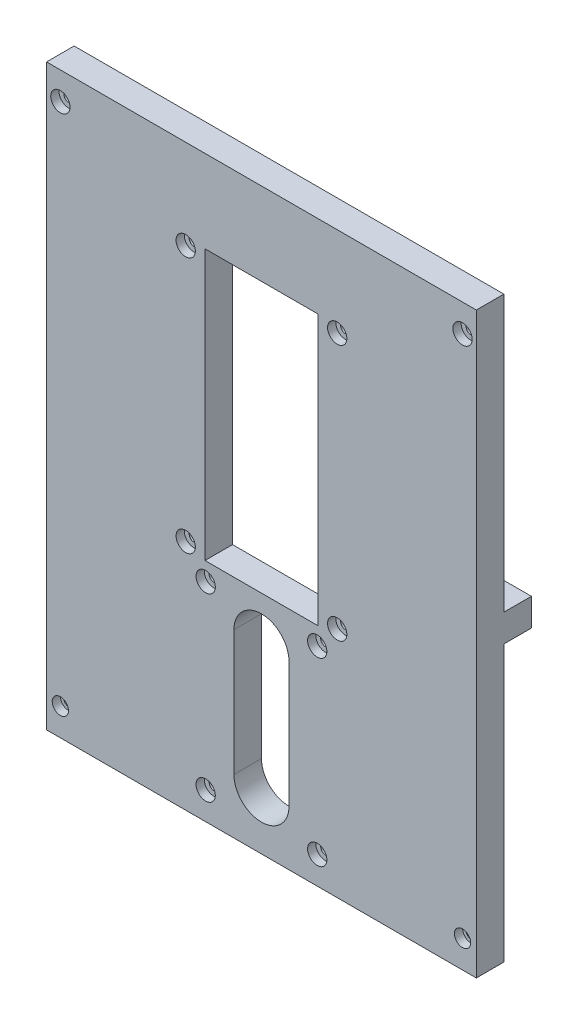
SolidWorks part; units mm, degrees
ref_plane "Płaszczyzna przednia" through (0, 0, 0) normal (0, 0, 1) x (1, 0, 0)
ref_plane "Płaszczyzna górna" through (0, 0, 0) normal (0, 1, 0) x (1, 0, 0)
ref_plane "Płaszczyzna prawa" through (0, 0, 0) normal (1, 0, 0) x (0, 0, -1)
sketch "Sketch1" plane through (0, 0, 0) normal (0, 0, 1) x (1, 0, 0)
  line L1 (-78, 105) -> (78, 105)
  line L2 (-78, 105) -> (-78, -105)
  line L3 (-78, -105) -> (78, -105)
  line L4 (78, 105) -> (78, -105)
  line L5 (-78, 105) -> (78, -105) construction
  line L6 (-78, -105) -> (78, 105) construction
  point P0 (0, 0)
  dimension "D1" = 156
  dimension "D2" = 210
extrude "Boss-Extrude1" add sketch "Sketch1" along normal blind 10
sketch "Sketch2" plane through (0, 0, 0) normal (0, 0, 1) x (1, 0, 0)
  line L0 (-78, 0) -> (78, 0) construction
  line L1 (-78, 105) -> (-78, -105) construction
  line L2 (78, -105) -> (78, 105) construction
  line L3 (0, 0) -> (0, 17.7919) construction
  line L4 (-68, 5) -> (-78, 5)
  line L5 (-68, 5) -> (-68, -5)
  line L6 (-68, -5) -> (-78, -5)
  line L7 (-78, 5) -> (-78, -5)
  line L8 (-68, 5) -> (-78, -5) construction
  line L9 (-68, -5) -> (-78, 5) construction
  line L10 (68, -5) -> (78, 5) construction
  line L11 (68, 5) -> (78, -5) construction
  line L12 (78, 5) -> (78, -5)
  line L13 (68, -5) -> (78, -5)
  line L14 (68, 5) -> (68, -5)
  line L15 (68, 5) -> (78, 5)
  point P6 (-73, 0)
  point P18 (73, 0)
  dimension "D1" = 5
  dimension "D2" = 10
extrude "Boss-Extrude2" add sketch "Sketch2" against normal blind 10
sketch "Sketch3" plane through (0, 0, 0) normal (0, 0, 1) x (1, 0, 0)
  line L0 (78, 105) -> (-78, 105) construction
  line L1 (73, -95) -> (-73, -95) construction
  line L2 (73, -95) -> (73, 95) construction
  line L3 (73, 95) -> (-73, 95) construction
  line L4 (-73, -95) -> (-73, 95) construction
  line L5 (73, -95) -> (-73, 95) construction
  line L6 (73, 95) -> (-73, -95) construction
  line L7 (78, -105) -> (78, 105) construction
  circle A0 centre (-73, 95) radius 1.75
  circle A1 centre (73, 95) radius 1.75
  circle A2 centre (73, -95) radius 1.75
  circle A3 centre (-73, -95) radius 1.75
  point P0 (0, 0)
  dimension "D3" = 3.5
  dimension "D1" = 10
  dimension "D2" = 5
extrude "Cut-Extrude1" cut sketch "Sketch3" against normal through all both and the other way through all
sketch "Sketch4" plane through (0, 0, 0) normal (0, 0, 1) x (1, 0, 0)
  circle A0 centre (-73, 95) radius 3.5
  circle A1 centre (73, 95) radius 3.5
  circle A2 centre (73, -95) radius 2.9526
  circle A3 centre (-73, -95) radius 2.9538
  dimension "D1" = 7
extrude "Cut-Extrude2" cut sketch "Sketch4" against normal blind 3 from surface at 10 starting at face at (-71.25, -95, 10)
sketch "Sketch5" plane through (0, 0, 0) normal (0, 0, 1) x (1, 0, 0)
  line L0 (78, 105) -> (-78, 105) construction
  line L1 (-20.5, 75) -> (20.5, 75)
  line L2 (-20.5, 75) -> (-20.5, -23)
  line L3 (-20.5, -23) -> (20.5, -23)
  line L4 (20.5, 75) -> (20.5, -23)
  line L5 (-20.5, 75) -> (20.5, -23) construction
  line L6 (-20.5, -23) -> (20.5, 75) construction
  line L7 (-27.5, 72.5) -> (27.5, 72.5) construction
  line L8 (-27.5, 72.5) -> (-27.5, -20.5) construction
  line L9 (-27.5, -20.5) -> (27.5, -20.5) construction
  line L10 (27.5, 72.5) -> (27.5, -20.5) construction
  line L11 (-27.5, 72.5) -> (27.5, -20.5) construction
  line L12 (-27.5, -20.5) -> (27.5, 72.5) construction
  line L13 (0, 26) -> (0, -105) construction
  line L14 (-78, -105) -> (78, -105) construction
  line L15 (0, -39.5) -> (0, -85) construction
  line L16 (10, -39.5) -> (10, -85)
  line L17 (-10, -39.5) -> (-10, -85)
  line L19 (-20.25, -95) -> (20.25, -95) construction
  line L20 (-20.25, -95) -> (-20.25, -29.5) construction
  line L21 (-20.25, -29.5) -> (20.25, -29.5) construction
  line L22 (20.25, -95) -> (20.25, -29.5) construction
  line L23 (-20.25, -95) -> (20.25, -29.5) construction
  line L24 (-20.25, -29.5) -> (20.25, -95) construction
  circle A0 centre (-27.5, 72.5) radius 1.75
  circle A1 centre (27.5, 72.5) radius 1.75
  circle A2 centre (27.5, -20.5) radius 1.75
  circle A3 centre (-27.5, -20.5) radius 1.75
  arc A4 (10, -39.5) -> (-10, -39.5) centre (0, -39.5) ccw
  arc A5 (-10, -85) -> (10, -85) centre (0, -85) ccw
  circle A6 centre (-20.25, -29.5) radius 1.75
  circle A7 centre (20.25, -29.5) radius 1.75
  circle A8 centre (20.25, -95) radius 1.75
  circle A9 centre (-20.25, -95) radius 1.75
  point P0 (0, 26)
  point P7 (0, 26)
  point P23 (0, -62.25)
  point P28 (0, -62.25)
  dimension "D5" = 3.5
  dimension "D1" = 41
  dimension "D2" = 98
  dimension "D3" = 93
  dimension "D4" = 55
  dimension "D6" = 30
  dimension "D7" = 65.5
  dimension "D8" = 40.5
  dimension "D9" = 20
  dimension "D10" = 10
extrude "Cut-Extrude3" cut sketch "Sketch5" against normal through all both and the other way through all
sketch "Sketch6" plane through (0, 0, 0) normal (0, 0, 1) x (1, 0, 0)
  circle A0 centre (-20.25, -95) radius 3.5
  circle A1 centre (20.25, -95) radius 3.5
  circle A2 centre (20.25, -29.5) radius 3.5
  circle A3 centre (-20.25, -29.5) radius 3.5
  circle A4 centre (27.5, -20.5) radius 3.5
  circle A5 centre (-27.5, -20.5) radius 3.5
  circle A6 centre (-27.5, 72.5) radius 3.5
  circle A7 centre (27.5, 72.5) radius 3.5
  dimension "D1" = 7
extrude "Cut-Extrude4" cut sketch "Sketch6" against normal blind 3 from surface at 10 starting at face at (-25.75, 72.5, 10)
